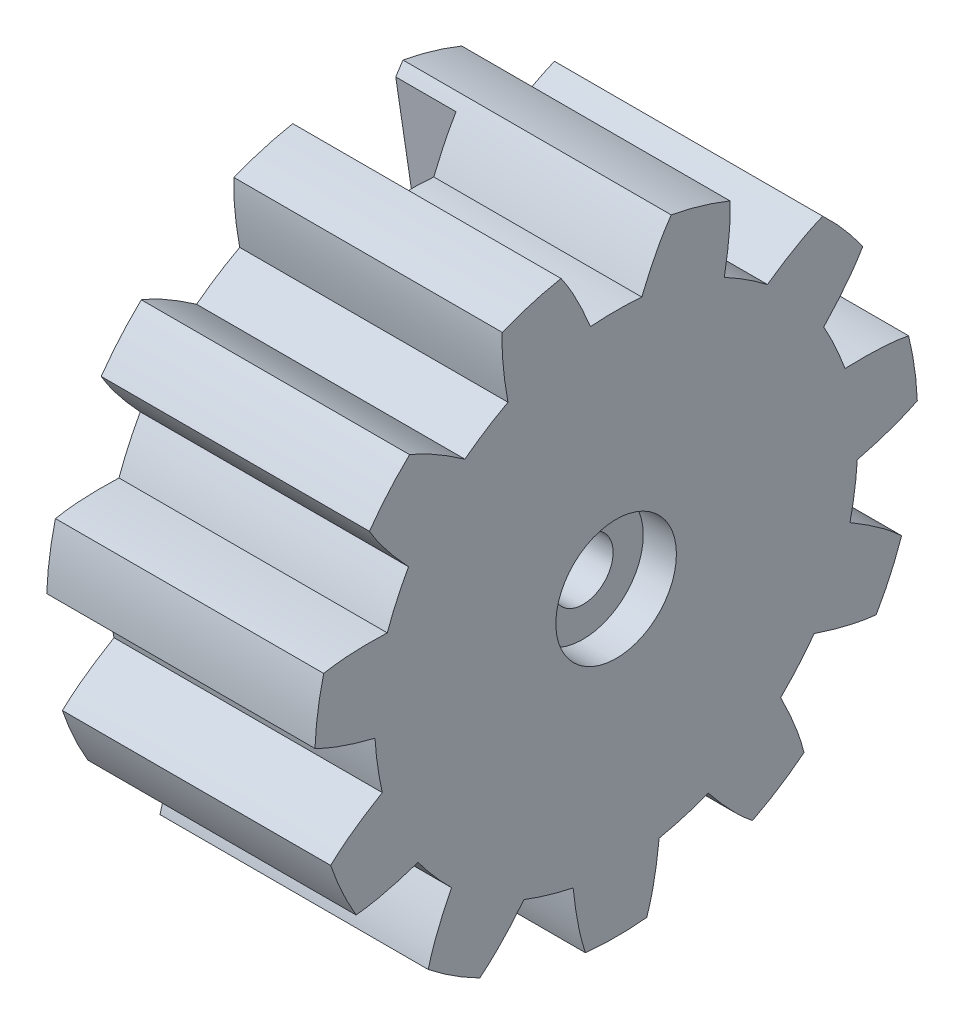
SolidWorks part; units mm, degrees
ref_plane "Front Plane" through (0, 0, 0) normal (0, 0, 1) x (1, 0, 0)
ref_plane "Top Plane" through (0, 0, 0) normal (0, 1, 0) x (1, 0, 0)
ref_plane "Right Plane" through (0, 0, 0) normal (1, 0, 0) x (0, 0, -1)
sketch "Sketch2" plane through (0, 0, 0) normal (1, 0, 0) x (0, 0, -1)
  circle A0 centre (0, 0) radius 10
  arc A1 (2.2589, 9.7415) -> (-2.2589, 9.7415) centre (0, 0) ccw
  circle A2 centre (0, 0) radius 1
  dimension "D1" = 2
extrude "Boss-Extrude2" add sketch "Sketch2" along normal blind 8.9 contours A0 A2
sketch "Sketch6" plane through (0, 0, 0) normal (1, 0, 0) x (0, 0, -1)
  line L0 (0, 12.3083) -> (0, 3.6493) construction
  line L2 (0.7584, 10.2947) -> (-0.7596, 10.2947)
  line L3 (0.7584, 10.2947) -> (0.7584, 9.6777)
  line L4 (0.7584, 9.6777) -> (-0.7596, 9.6777)
  line L5 (-0.7596, 10.2947) -> (-0.7596, 9.6777)
  arc A0 (1.85, 9.8631) -> (-1.85, 9.8631) centre (0, -2.6355) ccw
  arc A2 (0.85, 7.9604) -> (-0.85, 7.9604) centre (0, -2.6355) ccw
  spline S0 degree 3 poles (0.85, 7.9604) (1.1333, 8.6456) (1.4465, 9.2999) (1.85, 9.8631) knots 0.309355 0.309355 0.309355 0.309355 0.515064 0.515064 0.515064 0.515064
  spline S1 degree 3 poles (-0.85, 7.9604) (-1.1333, 8.6456) (-1.4465, 9.2999) (-1.85, 9.8631) knots 0.309355 0.309355 0.309355 0.309355 0.515064 0.515064 0.515064 0.515064
  dimension "D1" = 1.7
  dimension "D2" = 3.7
extrude "Cut-Extrude4" cut sketch "Sketch6" along normal blind 10 contours A0 L0 A2 S0 | L0 A0 S1 A2 | A0 L0 L4 L3 | L0 A0 L5 L4 | L2 L0 A0 L3 | L0 L2 L5 A0
pattern_circular "CirPattern2" count 11 over 360 about axis through (8.9, 0, 0) along (-1, 0, 0) of "Cut-Extrude4"
sketch "Sketch9" plane through (0, 0, 0) normal (-1, 0, 0) x (0, 0, 1)
  line L0 (-3, 0) -> (3, 0) construction
  line L1 (-1.3559, 11.0229) -> (1.3559, 11.0229)
  line L2 (1.3559, 11.0229) -> (3, 0)
  line L3 (-3, 0) -> (-1.3559, 11.0229)
  circle A0 centre (0, 0) radius 3.5
  point P4 (0, 0)
  point P7 (0, 7.4955)
  circle M2 centre (0, 0) radius 1
  spline M8 degree 3 poles (1.85, 9.8631) (1.4465, 9.2999) (1.1333, 8.6456) (0.85, 7.9604) knots 0.309355 0.309355 0.309355 0.309355 0.515064 0.515064 0.515064 0.515064 only from (1.8276, 9.8316) to (0.85, 7.9604)
  arc M9 (0.85, 7.9604) -> (-0.85, 7.9604) centre (0, -2.6355) ccw
  spline M10 degree 3 poles (-0.85, 7.9604) (-1.1333, 8.6456) (-1.4465, 9.2999) (-1.85, 9.8631) knots 0.309355 0.309355 0.309355 0.309355 0.515064 0.515064 0.515064 0.515064 only from (-0.85, 7.9604) to (-1.8276, 9.8316)
  dimension "D1" = 7
  dimension "D2" = 6
extrude "Cut-Extrude6" cut sketch "Sketch9" against normal blind 2 contours L0 L3 A0 L2 M2 | L3 L0 L2 A0 M2 | A0 L2 L3 M8 M9 M10
sketch "Sketch7" plane through (8.9, 0, 0) normal (1, 0, 0) x (0, 0, -1)
  circle A0 centre (0, 0) radius 1 construction
  circle A1 centre (0, 0) radius 1
  circle A2 centre (0, 0) radius 2
extrude "Cut-Extrude5" cut sketch "Sketch7" against normal blind 1.1
